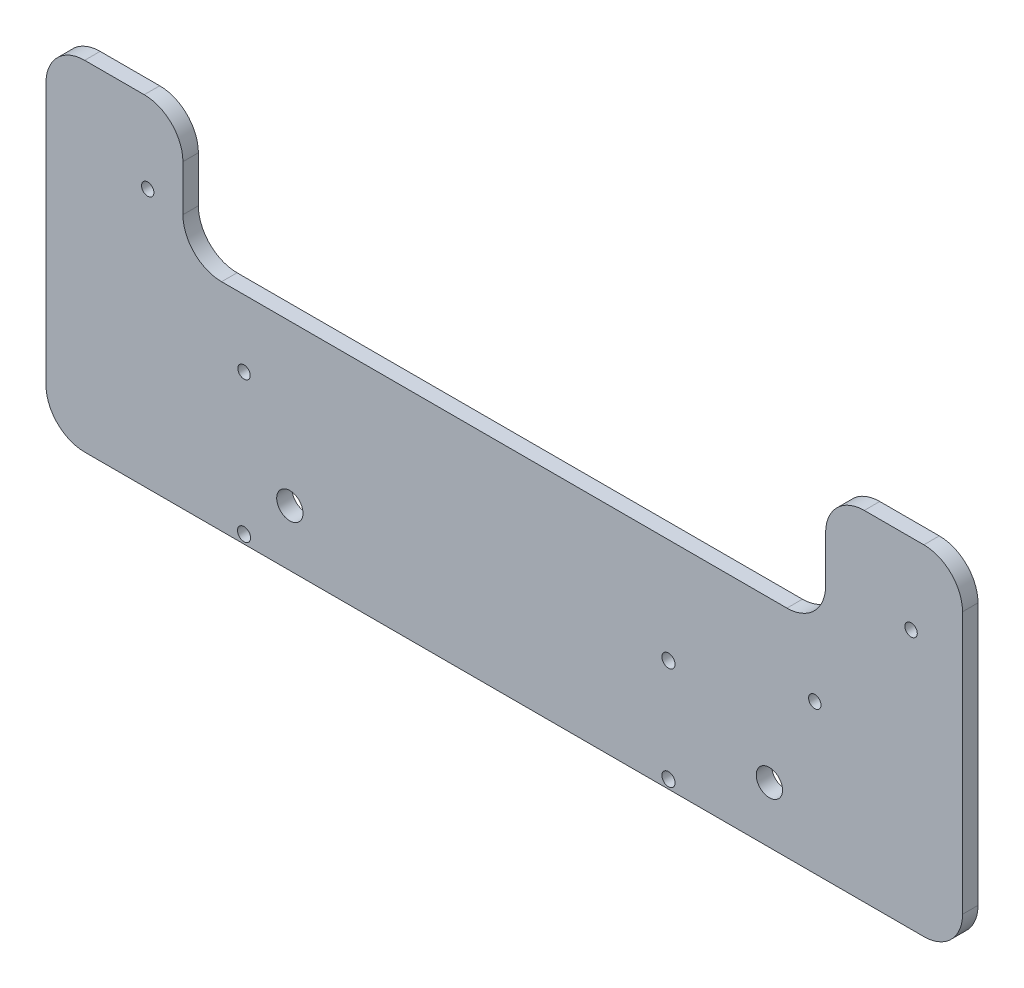
SolidWorks part; units mm, degrees
ref_plane "Front Plane" through (0, 0, 0) normal (0, 0, 1) x (1, 0, 0)
ref_plane "Top Plane" through (0, 0, 0) normal (0, 1, 0) x (1, 0, 0)
ref_plane "Right Plane" through (0, 0, 0) normal (1, 0, 0) x (0, 0, -1)
sketch "Sketch1" plane through (0, 0, 0) normal (0, 0, 1) x (1, 0, 0)
  line L0 (128.6273, -305.6657) -> (128.6273, -359.4647)
  line L1 (128.6273, -359.4647) -> (-108.3727, -359.4647)
  line L2 (-72.9682, -271.7188) -> (-72.9682, -303.5973)
  line L3 (128.6273, -305.6657) -> (128.6273, -271.7188)
  line L4 (128.6273, -271.7188) -> (93.2228, -271.7188)
  line L5 (93.2228, -271.7188) -> (93.2228, -303.5973)
  line L6 (93.2228, -303.5973) -> (-72.9682, -303.5973)
  line L7 (10.1273, -359.4647) -> (10.1273, -155.0286) construction
  line L8 (-108.3727, -271.7188) -> (-72.9682, -271.7188)
  line L9 (-108.3727, -305.6657) -> (-108.3727, -271.7188)
  line L10 (-108.3727, -305.6657) -> (-108.3727, -359.4647)
  point P5 (10.1273, -303.5973)
extrude "Boss-Extrude1" add sketch "Sketch1" along normal blind 4
hole_wizard "M3 Clearance Hole1" positions "Sketch3" profile "Sketch2" hole size "M3" standard "ISO" end condition through all
sketch "Sketch3" plane through (0, 0, 4) normal (0, 0, 1) x (1, 0, 0)
  point P0 (-82.0727, -292.4157)
  point P2 (115.3273, -292.4157)
  point P8 (90.4173, -320.9157)
  point P10 (-57.1627, -320.9157)
sketch "Sketch2" plane through (-82.0727, -292.4157, 4) normal (1, 0, 0) x (0, -1, 0)
  line L0 (0, 0) -> (0, 4)
  line L1 (0, 4) -> (1.6, 4)
  line L2 (1.6, 4) -> (1.6, 0)
  line L5 (1.6, 0) -> (0, 0)
  line L11 (0, -6.35) -> (0, 107.95) construction
  dimension "Thru Hole Dia." = 3.2
  dimension "Thru Hole Depth" = 4
fillet "Fillet1" radius 10 8 edges at (-108.3727, -359.4647, 2) (128.6273, -359.4647, 2) (128.6273, -271.7188, 2) (93.2228, -271.7188, 2) (93.2228, -303.5973, 2) (-108.3727, -271.7188, 2) (-72.9682, -303.5973, 2) (-72.9682, -271.7188, 2)
hole_wizard "Tap Drill for M8 Tap1" positions "Sketch5" profile "Sketch4" hole size "M8" standard "ISO" end condition through all
sketch "Sketch5" plane through (0, 0, 4) normal (0, 0, 1) x (1, 0, 0)
  point P4 (78.681, -344.9355)
  point P6 (-45.319, -344.9355)
sketch "Sketch4" plane through (78.681, -344.9355, 4) normal (1, 0, 0) x (0, -1, 0)
  line L0 (0, 0) -> (0, 4)
  line L1 (0, 4) -> (3.4, 4)
  line L2 (3.4, 4) -> (3.4, 0)
  line L5 (3.4, 0) -> (0, 0)
  line L11 (0, -6.35) -> (0, 107.95) construction
  dimension "Thru Hole Dia." = 6.8
  dimension "Thru Hole Depth" = 4
hole_wizard "M3 Clearance Hole3" positions "Sketch9" profile "Sketch8" hole size "M3" standard "ISO" end condition through all
sketch "Sketch9" plane through (0, 0, 4) normal (0, 0, 1) x (1, 0, 0)
  line L0 (52.5925, -330.6657) -> (52.5925, -368.9276) construction
  line L1 (52.5925, -357.2268) -> (-134.7708, -357.2268) construction
  line L2 (-57.1627, -320.9157) -> (-57.1627, -495.9346) construction
  point P0 (52.5925, -330.6657)
  point P7 (52.5925, -357.2268)
  point P21 (-57.1627, -357.2268)
sketch "Sketch8" plane through (52.5925, -330.6657, 4) normal (1, 0, 0) x (0, -1, 0)
  line L0 (0, 0) -> (0, 4)
  line L1 (0, 4) -> (1.7, 4)
  line L2 (1.7, 4) -> (1.7, 0)
  line L5 (1.7, 0) -> (0, 0)
  line L11 (0, -6.35) -> (0, 107.95) construction
  dimension "Thru Hole Dia." = 3.4
  dimension "Thru Hole Depth" = 4
